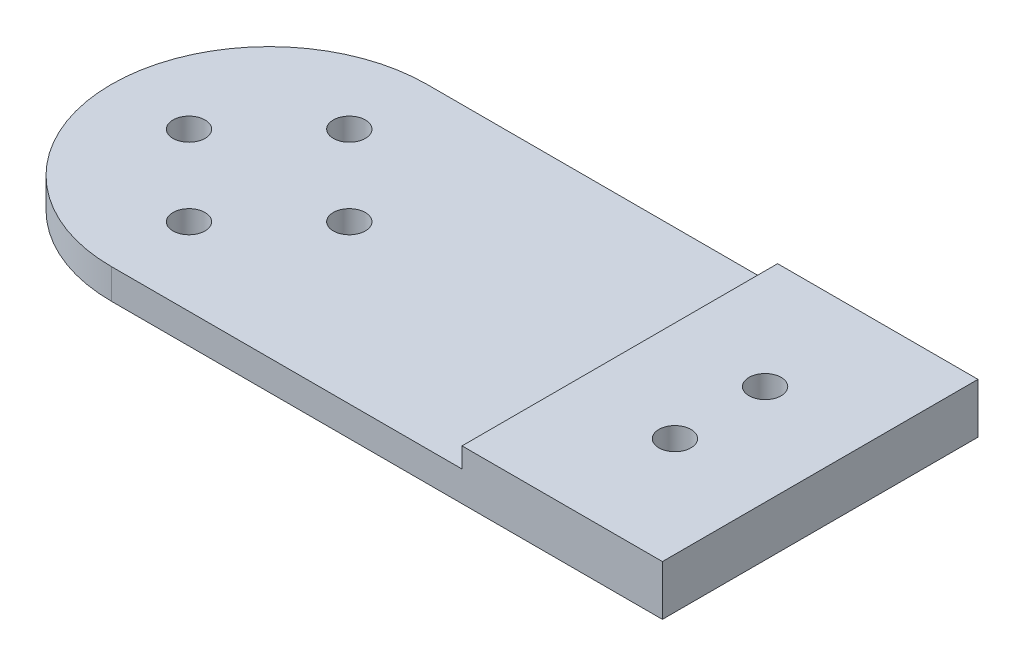
SolidWorks part; units mm, degrees
ref_plane "前视基准面" through (0, 0, 0) normal (0, 0, 1) x (1, 0, 0)
ref_plane "上视基准面" through (0, 0, 0) normal (0, 1, 0) x (1, 0, 0)
ref_plane "右视基准面" through (0, 0, 0) normal (1, 0, 0) x (0, 0, -1)
sketch "草图1" plane through (0, 0, 0) normal (0, 1, 0) x (1, 0, 0)
  line L0 (0, 0) -> (0, 12.2184) construction
  line L1 (0, 0) -> (14.977, 0) construction
  circle A0 centre (0, 0) radius 15.75
  circle A1 centre (0, 8) radius 1.6
  circle A2 centre (8, 0) radius 1.6
  circle A3 centre (0, -8) radius 1.6
  circle A4 centre (-8, 0) radius 1.6
  dimension "D1" = 31.5
  dimension "D4" = 3.2
  dimension "D5" = 3.2
  dimension "D2" = 8
  dimension "D3" = 8
extrude "凸台-拉伸1" add sketch "草图1" along normal blind 3
sketch "草图2" plane through (0, 0, 0) normal (0, -1, 0) x (1, 0, 0)
  line L1 (0, 15.75) -> (55, 15.75)
  line L3 (0, -15.75) -> (55, -15.75)
  line L4 (55, 15.75) -> (55, -15.75)
  circle A0 centre (0, 0) radius 15.75 construction
  arc A1 (0, -15.75) -> (0, 15.75) centre (0, 0) ccw
  dimension "D1" = 55
extrude "凸台-拉伸2" add sketch "草图2" against normal blind 3
sketch "草图3" plane through (0, 0, 0) normal (0, -1, 0) x (1, 0, 0)
  line L0 (0, -15.75) -> (55, -15.75) construction
  line L1 (55, 15.75) -> (35, 15.75)
  line L2 (55, 15.75) -> (55, -15.75)
  line L3 (55, -15.75) -> (35, -15.75)
  line L4 (35, 15.75) -> (35, -15.75)
  dimension "D1" = 20
extrude "凸台-拉伸3" add sketch "草图3" against normal blind 5
sketch "草图4" plane through (0, 5, 0) normal (0, 1, 0) x (1, 0, 0)
  line L0 (18.4528, 0) -> (59.3342, 0) construction
  line L1 (55, 15.75) -> (55, -15.75) construction
  circle A0 centre (45, 4.5) radius 1.6
  circle A1 centre (45, -4.5) radius 1.6
  dimension "D1" = 9
  dimension "D2" = 10
  dimension "D3" = 3.2
extrude "切除-拉伸1" cut sketch "草图4" against normal blind 10
